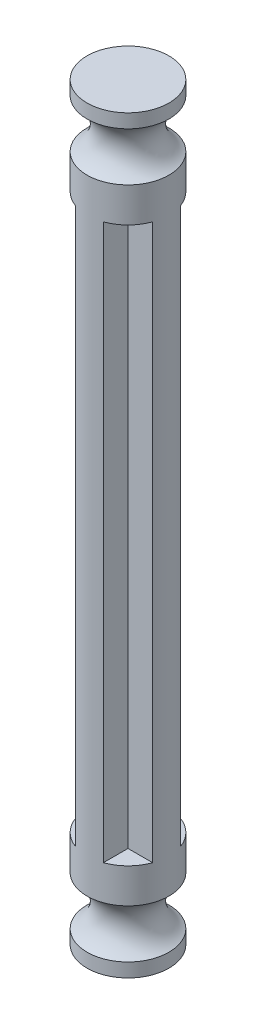
SolidWorks part; units mm, degrees
ref_plane "前视基准面" through (0, 0, 0) normal (0, 0, 1) x (1, 0, 0)
ref_plane "上视基准面" through (0, 0, 0) normal (0, 1, 0) x (1, 0, 0)
ref_plane "右视基准面" through (0, 0, 0) normal (1, 0, 0) x (0, 0, -1)
sketch "草图1" plane through (0, 0, 0) normal (0, 1, 0) x (1, 0, 0)
  line L0 (1, 1) -> (1, 2.7753)
  line L7 (1, 1) -> (2.7753, 1)
  line L8 (1, -1) -> (2.7753, -1)
  line L9 (1, -1) -> (1, -2.7753)
  line L10 (-1, -1) -> (-1, -2.7753)
  line L11 (-1, -1) -> (-2.7753, -1)
  line L12 (-1, 1) -> (-2.7753, 1)
  line L13 (-1, 1) -> (-1, 2.7753)
  arc A0 (-2.7753, 1) -> (-2.7753, -1) centre (0, 0) ccw
  arc A1 (-1, -2.7753) -> (1, -2.7753) centre (0, 0) ccw
  arc A2 (2.7753, -1) -> (2.7753, 1) centre (0, 0) ccw
  arc A3 (1, 2.7753) -> (-1, 2.7753) centre (0, 0) ccw
  dimension "D1" = 5.9
  dimension "D2" = 2
  dimension "D3" = 2
  dimension "D4" = 2
  dimension "D5" = 2
  dimension "D6" = 1
  dimension "D7" = 1
  dimension "D8" = 1
  dimension "D9" = 1
extrude "凸台-拉伸2" add sketch "草图1" along normal blind 40
sketch "草图3" plane through (0, 0, 0) normal (1, 0, 0) x (0, 0, -1)
  line L0 (0, 40) -> (0, 47)
  line L1 (1, 40) -> (-1, 40) construction
  line L2 (0, 47) -> (2.95, 47)
  line L3 (0, 40) -> (2.95, 40)
  line L4 (2.95, 40) -> (2.95, 42.5)
  line L5 (2.95, 47) -> (2.95, 46)
  line L6 (0, 0) -> (0, -7)
  line L7 (0, -7) -> (2.95, -7)
  line L8 (0, 0) -> (2.95, 0)
  line L9 (2.95, 0) -> (2.95, -2.5)
  line L10 (2.95, -7) -> (2.95, -6)
  arc A0 (2.95, 46) -> (2.95, 42.5) centre (3.9182, 44.25) ccw
  arc A1 (2.95, -2.5) -> (2.95, -6) centre (3.9182, -4.25) ccw
  dimension "D5" = 1
  dimension "D4" = 2
  dimension "D9" = 2
  dimension "D1" = 2.95
  dimension "D2" = 7
  dimension "D3" = 2.5
  dimension "D6" = 7
  dimension "D7" = 2.5
  dimension "D8" = 1
revolve "旋转3" add sketch "草图3" angle 360 about L6
